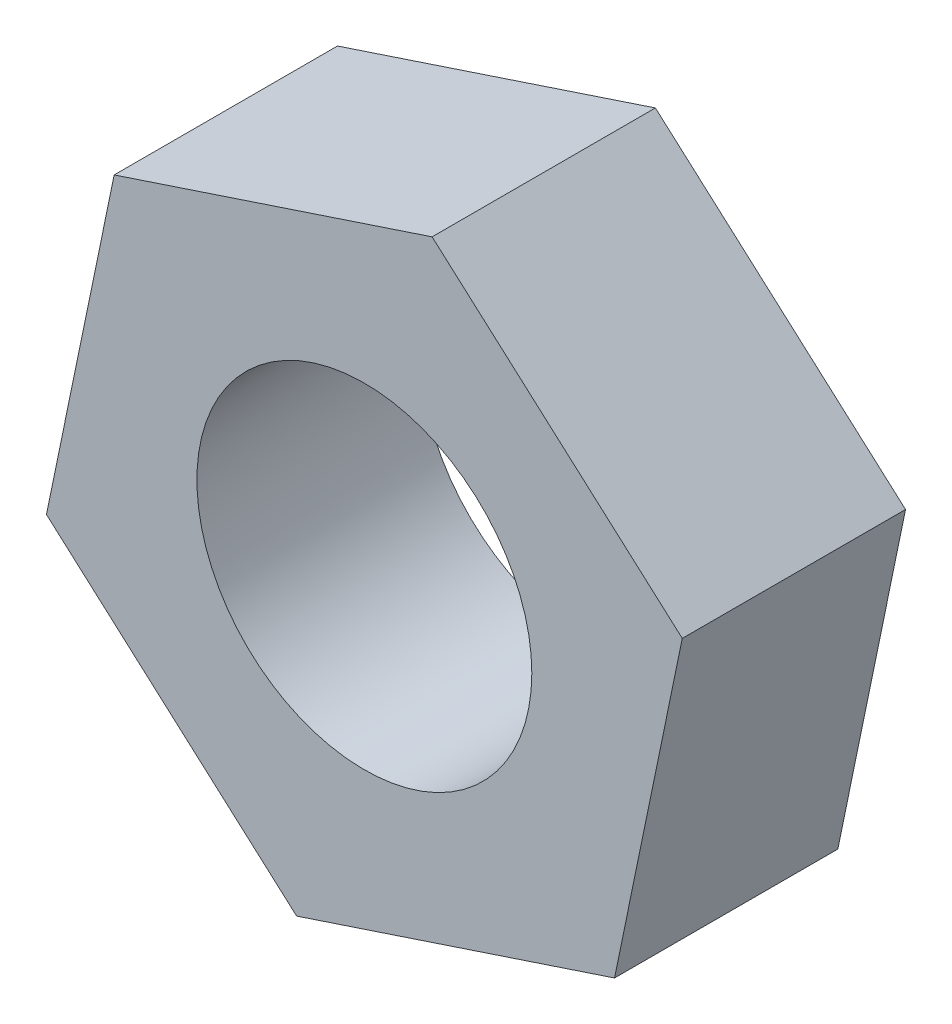
SolidWorks part; units mm, degrees
ref_plane "Front Plane" through (0, 0, 0) normal (0, 0, 1) x (1, 0, 0)
ref_plane "Top Plane" through (0, 0, 0) normal (0, 1, 0) x (1, 0, 0)
ref_plane "Right Plane" through (0, 0, 0) normal (1, 0, 0) x (0, 0, -1)
sketch "Sketch1" plane through (0, 0, 0) normal (0, 0, 1) x (1, 0, 0)
  line L1 (-0.6068, -2.938) -> (2.241, -1.9945)
  line L2 (2.241, -1.9945) -> (2.8478, 0.9435)
  line L3 (2.8478, 0.9435) -> (0.6068, 2.938)
  line L4 (0.6068, 2.938) -> (-2.241, 1.9945)
  line L5 (-2.241, 1.9945) -> (-2.8478, -0.9435)
  line L6 (-2.8478, -0.9435) -> (-0.6068, -2.938)
  circle A0 centre (0, 0) radius 2.5981 construction
  circle A1 centre (0, 0) radius 1.5
  dimension "D1" = 3
extrude "Extrude2" add sketch "Sketch1" along normal blind 2
